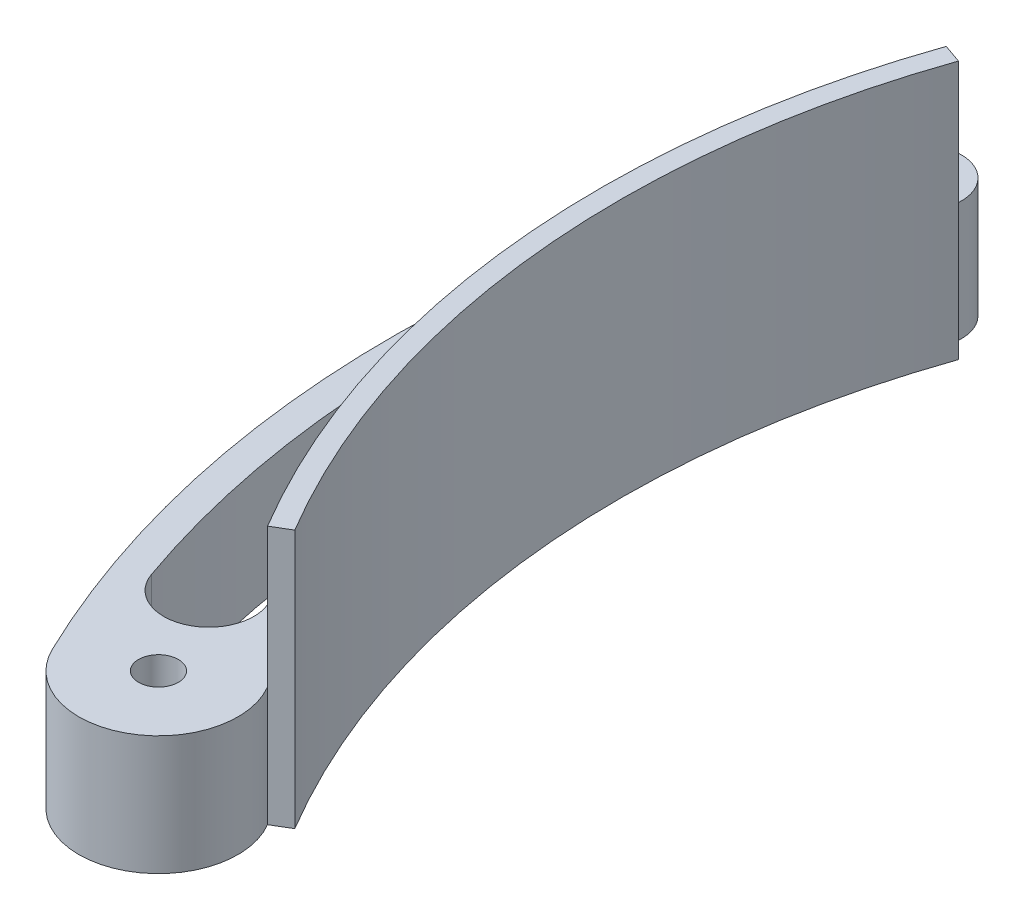
SolidWorks part; units mm, degrees
material "6061-T6 (SS)"
ref_plane "Front Plane" through (0, 0, 0) normal (0, 0, 1) x (1, 0, 0)
ref_plane "Top Plane" through (0, 0, 0) normal (0, 1, 0) x (1, 0, 0)
ref_plane "Right Plane" through (0, 0, 0) normal (1, 0, 0) x (0, 0, -1)
sketch "Sketch1" plane through (0, 0, 0) normal (0, 1, 0) x (1, 0, 0)
  line L5 (-134.0196, -92.456) -> (-46.5467, -92.456) construction
  line L6 (0, -143.256) -> (-105.4914, -143.256) construction
  circle A0 centre (0, 0) radius 143.256 construction
  arc A1 (-135.2523, 47.2132) -> (-123.106, -73.2612) centre (0, 0) ccw
  circle A2 centre (-134.0196, -79.756) radius 3.175
  arc A3 (-123.106, -73.2612) -> (-145.4546, -85.2815) centre (-134.0196, -79.756) cw
  arc A4 (-145.4546, -85.2815) -> (-147.0269, 51.937) centre (0, -14.9966) cw
  arc A5 (-147.0269, 51.937) -> (-135.2523, 47.2132) centre (-141.2476, 49.306) cw
  circle A6 centre (-152.2388, -5.7661) radius 3.175
  circle A7 centre (-152.2388, -5.7661) radius 12.7 construction
  arc A8 (-141.2476, 49.306) -> (-134.0196, -79.756) centre (0, -7.517) ccw construction
  dimension "D1" = 286.512
  dimension "D2" = 6.35
  dimension "D3" = 12.7
  dimension "D4" = 6.35
  dimension "D6" = 6.35
  dimension "D7" = 9.525
  dimension "D5" = 63.5
  dimension "D10" = 50
  dimension "D11" = 76.2
extrude "Boss-Extrude1" add sketch "Sketch1" along normal blind 19.05
sketch "Sketch2" plane through (0, 19.05, 0) normal (0, 1, 0) x (1, 0, 0)
  arc A0 (-143.4148, 50.2926) -> (-138.9993, 48.5212) centre (-141.2476, 49.306) cw
  arc A1 (-147.0124, 7.9044) -> (-155.7687, 8.8066) centre (-151.4127, 8.141) cw
  circle A2 centre (-152.2388, -5.7661) radius 9.525 construction
  circle A3 centre (-152.2388, -5.7661) radius 3.175 construction
  arc A4 (-135.2523, 47.2132) -> (-123.106, -73.2612) centre (0, 0) ccw construction
  arc A5 (-147.0269, 51.937) -> (-145.4546, -85.2815) centre (0, -14.9966) ccw construction
  arc A6 (-135.2523, 47.2132) -> (-147.0269, 51.937) centre (-141.2476, 49.306) ccw construction
  arc A9 (-138.9993, 48.5212) -> (-147.0124, 7.9044) centre (0, 0) ccw
  arc A12 (-143.4148, 50.2926) -> (-155.7687, 8.8066) centre (0, -14.9966) ccw
  dimension "D3" = 6.35
  dimension "D1" = 2.3813
extrude "Cut-Extrude1" cut sketch "Sketch2" against normal through all
sketch "Sketch4" plane through (0, 19.05, 0) normal (0, 1, 0) x (1, 0, 0)
  line L0 (-151.6785, -20.2971) -> (-152.2388, -5.7661) construction
  line L1 (-141.1195, -64.6207) -> (-134.0196, -79.756) construction
  arc A2 (-139.7487, 48.7828) -> (-127.1986, -75.6968) centre (0, 0) ccw
  arc A3 (-146.7108, -19.6323) -> (-134.5797, -61.6261) centre (0, 0) ccw
  arc A4 (-156.6875, -20.4722) -> (-146.7108, -19.6323) centre (-151.6785, -20.2971) cw
  arc A5 (-142.6924, 49.9638) -> (-141.1665, -83.2094) centre (0, -14.9966) ccw
  arc A6 (-156.6875, -20.4722) -> (-147.905, -67.0068) centre (0, -14.9966) ccw
  arc A7 (-147.905, -67.0068) -> (-134.5797, -61.6261) centre (-141.1195, -64.6207) ccw
  circle A8 centre (-152.2388, -5.7661) radius 3.175 construction
  circle A9 centre (-134.0196, -79.756) radius 3.175 construction
  point P0 (-151.8716, -15.2888)
  point P13 (-152.1165, -8.9388)
  point P14 (-138.0648, -71.1327)
  point P20 (-135.368, -76.8816)
  dimension "D3" = 6.35
  dimension "D4" = 6.35
  dimension "D1" = 4.7625
  dimension "D2" = 4.7625
extrude "Cut-Extrude2" cut sketch "Sketch4" against normal through all
sketch "Sketch3" plane through (0, 0, 0) normal (0, 1, 0) x (1, 0, 0)
  line L0 (-123.106, -73.2612) -> (-120.3775, -71.6375)
  line L1 (-132.2547, 46.1668) -> (-135.2523, 47.2132)
  arc A0 (-123.106, -73.2612) -> (-135.2523, 47.2132) centre (0, 0) cw
  arc A1 (-135.2523, 47.2132) -> (-123.106, -73.2612) centre (0, 0) ccw construction
  arc A2 (-120.3775, -71.6375) -> (-132.2547, 46.1668) centre (0, 0) cw
  circle A3 centre (-134.0196, -79.756) radius 3.175 construction
  arc A5 (-138.9993, 48.5212) -> (-143.4148, 50.2926) centre (-141.2476, 49.306) ccw construction
  point P10 (-134.0196, -79.756)
  point P14 (-141.2476, 49.306)
  dimension "D1" = 3.175
extrude "Boss-Extrude2" add sketch "Sketch3" along normal blind 41.275 separate body
